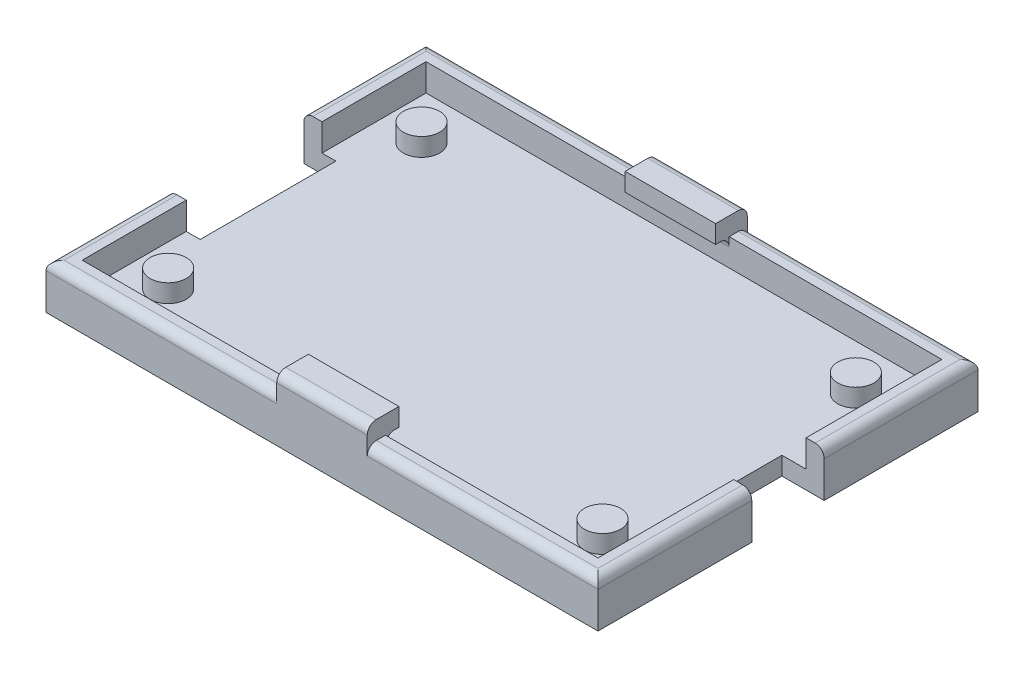
SolidWorks part; units mm, degrees
ref_plane "Front Plane" through (0, 0, 0) normal (0, 0, 1) x (1, 0, 0)
ref_plane "Top Plane" through (0, 0, 0) normal (0, 1, 0) x (1, 0, 0)
ref_plane "Right Plane" through (0, 0, 0) normal (1, 0, 0) x (0, 0, -1)
sketch "Sketch1" plane through (0, 0, 0) normal (0, 1, 0) x (1, 0, 0)
  line L1 (-20.7598, 19.0936) -> (40.2402, 19.0936)
  line L2 (-20.7598, 19.0936) -> (-20.7598, -22.9064)
  line L3 (-20.7598, -22.9064) -> (40.2402, -22.9064)
  line L4 (40.2402, 19.0936) -> (40.2402, -22.9064)
  dimension "D1" = 61
  dimension "D2" = 42
extrude "Boss-Extrude1" add sketch "Sketch1" along normal blind 2
sketch "Sketch2" plane through (0, 2, 0) normal (0, 1, 0) x (1, 0, 0)
  line L0 (-20.7598, 19.0936) -> (40.2402, 19.0936)
  line L1 (40.2402, 19.0936) -> (40.2402, -22.9064)
  line L2 (40.2402, -22.9064) -> (-20.7598, -22.9064)
  line L3 (-20.7598, -22.9064) -> (-20.7598, 19.0936)
  line L4 (-18.7598, 17.0936) -> (-18.7598, -20.9064)
  line L5 (-18.7598, -20.9064) -> (38.2402, -20.9064)
  line L6 (38.2402, -20.9064) -> (38.2402, 17.0936)
  line L7 (38.2402, 17.0936) -> (-18.7598, 17.0936)
  dimension "D1" = 2
  dimension "D2" = 2
  dimension "D3" = 2
  dimension "D4" = 2
extrude "Boss-Extrude2" add sketch "Sketch2" along normal blind 3
sketch "Sketch3" plane through (0, 5, 0) normal (0, 1, 0) x (1, 0, 0)
  line L0 (-20.7598, 19.0936) -> (-20.7598, -22.9064) construction
  line L1 (40.2402, -22.9064) -> (40.2402, 19.0936) construction
  line L3 (-22.9981, -9.4064) -> (-17.2228, -9.4064)
  line L4 (-22.9981, -9.4064) -> (-22.9981, 5.5936)
  line L5 (-22.9981, 5.5936) -> (-17.2228, 5.5936)
  line L6 (-17.2228, -9.4064) -> (-17.2228, 5.5936)
  line L7 (35.5729, -5.9064) -> (42.0276, -5.9064)
  line L8 (35.5729, -5.9064) -> (35.5729, 2.0936)
  line L9 (35.5729, 2.0936) -> (42.0276, 2.0936)
  line L10 (42.0276, -5.9064) -> (42.0276, 2.0936)
  point P0 (-20.7598, -1.9064)
  point P1 (40.2402, -1.9064)
  point P10 (-22.9981, -1.9064)
  point P15 (42.0276, -1.9064)
  dimension "D1" = 15
  dimension "D2" = 8
extrude "Cut-Extrude1" cut sketch "Sketch3" against normal blind 5
sketch "Sketch4" plane through (0, 2, 0) normal (0, 1, 0) x (1, 0, 0)
  line L1 (40.2402, 2.0936) -> (40.2402, -5.9064) construction
  line L2 (-18.7598, -9.4064) -> (-18.7598, 5.5936) construction
  circle A0 centre (-14.2598, -15.9064) radius 2
  circle A1 centre (-14.2598, 12.0936) radius 2
  circle A2 centre (33.7402, 12.0936) radius 2
  circle A3 centre (33.7402, -15.9064) radius 2
  point P8 (40.2402, -1.9064)
  point P11 (-18.7598, -1.9064)
  dimension "D1" = 4
  dimension "D2" = 28
  dimension "D3" = 28
  dimension "D4" = 14
  dimension "D5" = 14
  dimension "D6" = 48
  dimension "D7" = 48
  dimension "D8" = 4.5
extrude "Boss-Extrude3" add sketch "Sketch4" along normal blind 2
sketch "Sketch5" plane through (0, 5, 0) normal (0, 1, 0) x (1, 0, 0)
  line L0 (-20.7598, -22.9064) -> (40.2402, -22.9064) construction
  line L1 (4.7402, -22.9064) -> (14.7402, -22.9064)
  line L2 (4.7402, -22.9064) -> (4.7402, -19.4064)
  line L3 (4.7402, -19.4064) -> (14.7402, -19.4064)
  line L4 (14.7402, -22.9064) -> (14.7402, -19.4064)
  line L5 (40.2402, 19.0936) -> (-20.7598, 19.0936) construction
  line L6 (4.7402, 19.0936) -> (14.7402, 19.0936)
  line L7 (4.7402, 19.0936) -> (4.7402, 15.5936)
  line L8 (4.7402, 15.5936) -> (14.7402, 15.5936)
  line L9 (14.7402, 19.0936) -> (14.7402, 15.5936)
  point P12 (9.7402, -22.9064)
  point P13 (14.7402, 19.0936)
  point P14 (9.7402, -19.4064)
  point P15 (9.7402, 15.5936)
  dimension "D1" = 10
  dimension "D2" = 10
  dimension "D3" = 3.5
  dimension "D4" = 3.5
extrude "Boss-Extrude4" add sketch "Sketch5" along normal blind 2
fillet "Fillet1" radius 1 2 edges at (9.7402, 5, -17.0936) (9.7402, 5, 20.9064)
fillet "Fillet2" radius 1 9 edges at (40.2402, 5, 14.4064) (-20.7598, 5, 16.1564) (-20.7598, 5, -12.3436) (9.7402, 7, -19.0936) (9.7402, 7, 22.9064)
